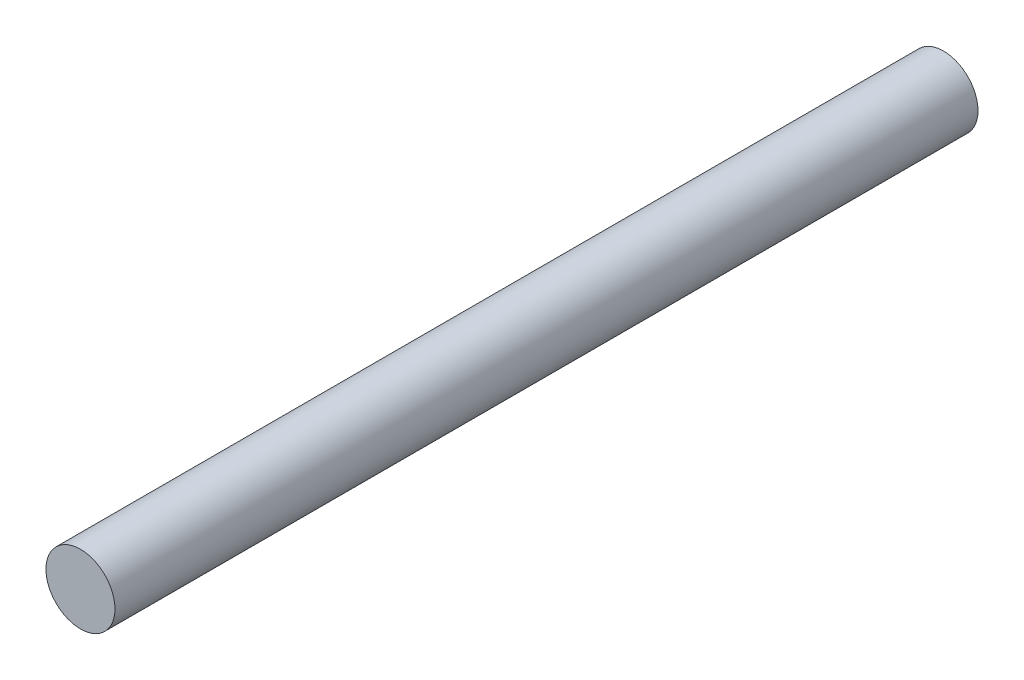
SolidWorks part; units mm, degrees
ref_plane "Front Plane" through (0, 0, 0) normal (0, 0, 1) x (1, 0, 0)
ref_plane "Top Plane" through (0, 0, 0) normal (0, 1, 0) x (1, 0, 0)
ref_plane "Right Plane" through (0, 0, 0) normal (1, 0, 0) x (0, 0, -1)
sketch "Sketch1" plane through (0, 0, 0) normal (0, 0, 1) x (1, 0, 0)
  circle A0 centre (-1.7556, 6.9078) radius 4
  dimension "D1" = 8
extrude "Boss-Extrude1" add sketch "Sketch1" along normal blind 100
